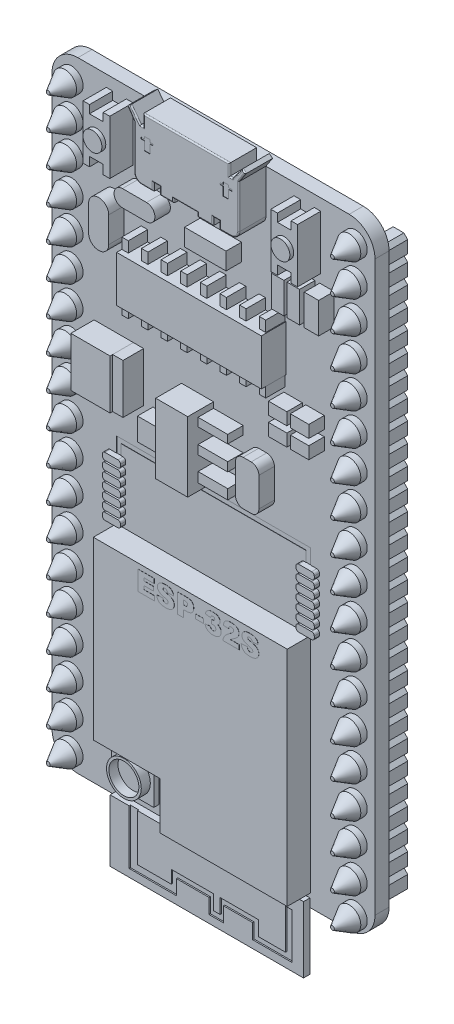
SolidWorks part; units mm, degrees
ref_plane "Front Plane" through (0, 0, 0) normal (0, 0, 1) x (1, 0, 0)
ref_plane "Top Plane" through (0, 0, 0) normal (0, 1, 0) x (1, 0, 0)
ref_plane "Right Plane" through (0, 0, 0) normal (1, 0, 0) x (0, 0, -1)
sketch "Sketch1" plane through (0, 0, 0) normal (0, 0, 1) x (1, 0, 0)
  line L1 (-10.5, 24) -> (10.5, 24)
  line L2 (-12.5, 22) -> (-12.5, -22)
  line L3 (-10.5, -24) -> (10.5, -24)
  line L4 (12.5, 22) -> (12.5, -22)
  line L5 (-12.5, 24) -> (12.5, -24) construction
  line L6 (-12.5, -24) -> (12.5, 24) construction
  arc A0 (-10.5, -24) -> (-12.5, -22) centre (-10.5, -22) cw
  arc A1 (10.5, -24) -> (12.5, -22) centre (10.5, -22) ccw
  arc A2 (12.5, 22) -> (10.5, 24) centre (10.5, 22) ccw
  arc A3 (-12.5, 22) -> (-10.5, 24) centre (-10.5, 22) cw
  point P0 (0, 0)
  dimension "D3" = 2
  dimension "D1" = 25
  dimension "D2" = 48
extrude "Boss-Extrude1" add sketch "Sketch1" along normal blind 1.09
sketch "Sketch2" plane through (0, 0, 1.09) normal (0, 0, 1) x (1, 0, 0)
  circle A0 centre (11.0006, 22.3012) radius 0.9
  dimension "D1" = 1.8
extrude "Boss-Extrude2" add sketch "Sketch2" along normal blind 1.8
chamfer "Chamfer1" distance 1.3 angle 30 1 edges at (11.9006, 22.3012, 2.89)
pattern_linear "LPattern1" count 19 spacing 2.5 along (0, -1, 0) count 2 spacing 22 along (-1, 0, 0) of "Boss-Extrude2", "Chamfer1"
sketch "Sketch3" plane through (0, 0, 1.09) normal (0, 0, 1) x (1, 0, 0)
  line L0 (0, 24) -> (0, -24)
  line L1 (-10.5, -24) -> (10.5, -24) construction
  line L2 (-12.5, 21.016) -> (12.5, 21.016)
  line L3 (12.5, -22) -> (12.5, 22) construction
  line L4 (-7.8022, 23.1053) -> (-7.8022, 22.482)
  line L5 (-8.3007, 23.1053) -> (-7.8022, 23.1053)
  line L6 (-8.3007, 23.1053) -> (-8.3007, 18.9267)
  line L7 (-8.3007, 18.9267) -> (-7.8022, 18.9267)
  line L8 (-6.2324, 23.1053) -> (-6.2324, 18.9267)
  line L9 (-8.3007, 23.1053) -> (-6.2324, 18.9267) construction
  line L10 (-8.3007, 18.9267) -> (-6.2324, 23.1053) construction
  line L11 (-7.8022, 22.482) -> (-6.7481, 22.482)
  line L12 (-6.7481, 22.482) -> (-6.7481, 23.1053)
  line L13 (-7.8022, 18.9267) -> (-7.8022, 19.6283)
  line L14 (-7.8022, 19.6283) -> (-6.7481, 19.6283)
  line L15 (-6.7481, 19.6283) -> (-6.7481, 18.9267)
  line L16 (-6.7481, 23.1053) -> (-6.2324, 23.1053)
  line L17 (-6.7481, 18.9267) -> (-6.2324, 18.9267)
  line L18 (8.3007, 18.9267) -> (6.2324, 23.1053) construction
  line L19 (8.3007, 23.1053) -> (6.2324, 18.9267) construction
  line L20 (6.7481, 18.9267) -> (6.2324, 18.9267)
  line L21 (6.7481, 23.1053) -> (6.2324, 23.1053)
  line L22 (6.7481, 19.6283) -> (6.7481, 18.9267)
  line L23 (7.8022, 19.6283) -> (6.7481, 19.6283)
  line L24 (7.8022, 18.9267) -> (7.8022, 19.6283)
  line L25 (6.7481, 22.482) -> (6.7481, 23.1053)
  line L26 (7.8022, 22.482) -> (6.7481, 22.482)
  line L27 (6.2324, 23.1053) -> (6.2324, 18.9267)
  line L28 (8.3007, 18.9267) -> (7.8022, 18.9267)
  line L29 (8.3007, 23.1053) -> (8.3007, 18.9267)
  line L30 (8.3007, 23.1053) -> (7.8022, 23.1053)
  line L31 (7.8022, 23.1053) -> (7.8022, 22.482)
  point P0 (-7.2666, 21.016)
  point P6 (0, 0)
  point P12 (0, 21.016)
  point P36 (7.2666, 21.016)
extrude "Boss-Extrude3" add sketch "Sketch3" along normal blind 1.8 contours L16 L12 L11 L4 L5 L6 L2 L8 | L15 L17 L8 L2 L6 L7 L13 L14 | L30 L31 L26 L25 L21 L27 L2 L29 | L29 L2 L27 L20 L22 L23 L24 L28
sketch "Sketch4" plane through (0, 0, 2.89) normal (0, 0, 1) x (1, 0, 0)
  line L0 (-7.2752, 22.482) -> (-7.2752, 19.6283) construction
  line L1 (-7.8022, 22.482) -> (-6.7481, 22.482) construction
  line L2 (-7.8022, 19.6283) -> (-6.7481, 19.6283) construction
  line L3 (-6.2324, 21.016) -> (-8.3007, 21.016) construction
  line L4 (-6.2324, 23.1053) -> (-6.2324, 18.9267) construction
  line L5 (-8.3007, 23.1053) -> (-8.3007, 18.9267) construction
  line L6 (0, 24) -> (0, 14.5911) construction
  line L7 (10.5, 24) -> (-10.5, 24) construction
  circle A0 centre (-7.2752, 21.0552) radius 0.7337
  circle A1 centre (7.2752, 21.0552) radius 0.7337
extrude "Boss-Extrude4" add sketch "Sketch4" along normal blind 0.3
sketch "Sketch5" plane through (0, 0, 1.09) normal (0, 0, 1) x (1, 0, 0)
  line L0 (-7.5049, -19.3526) -> (-2.3624, -19.3526)
  line L1 (-7.5049, -5.756) -> (7.5049, -5.756)
  line L2 (-7.5049, -5.756) -> (-7.5049, -19.3526)
  line L3 (-2.3624, -23.0043) -> (7.5049, -23.0043)
  line L4 (7.5049, -5.756) -> (7.5049, -23.0043)
  line L7 (-2.3624, -19.3526) -> (-2.3624, -23.0043)
  point P0 (0, -14.3801)
extrude "Boss-Extrude5" add sketch "Sketch5" along normal blind 1.8
sketch "Sketch6" plane through (0, 0, 2.89) normal (0, 0, 1) x (1, 0, 0)
  text T0 "ESP-32S" font "Arial Black" height 1.5
extrude "Boss-Extrude6" add sketch "Sketch6" along normal blind 0.01
sketch "Sketch7" plane through (0, 0, 1.09) normal (0, 0, 1) x (1, 0, 0)
  line L0 (-7.5049, -24) -> (-7.5049, -28.4731)
  line L1 (-10.5, -24) -> (10.5, -24) construction
  line L2 (-7.5049, -28.4731) -> (7.4655, -28.4731)
  line L3 (7.4655, -28.4731) -> (7.4655, -24)
  line L4 (-10.5, -24) -> (10.5, -24) construction
  line L5 (7.4655, -24) -> (7.4655, -23.3553)
  line L6 (7.4655, -23.3553) -> (-3.5697, -23.3553)
  line L7 (-3.5697, -23.3553) -> (-3.5697, -23.6776)
  line L8 (-3.5697, -23.6776) -> (-7.5049, -23.6776)
  line L9 (-7.5049, -23.6776) -> (-7.5049, -24)
extrude "Boss-Extrude7" add sketch "Sketch7" along normal blind 0.5
sketch "Sketch8" plane through (0, 0, 1.59) normal (0, 0, 1) x (1, 0, 0)
  line L0 (-6.0307, -23.6776) -> (-6.0307, -27.8761)
  line L1 (-3.5697, -23.6776) -> (-7.5049, -23.6776) construction
  line L2 (-6.0307, -27.8761) -> (-2.3778, -27.8761)
  line L3 (-2.3778, -27.8761) -> (-2.3778, -26.7276)
  line L4 (-2.3778, -26.7276) -> (0.1471, -26.7276)
  line L5 (0.1471, -26.7276) -> (0.1471, -27.8761)
  line L6 (0.1471, -27.8761) -> (1.2663, -27.8761)
  line L7 (1.2663, -27.8761) -> (1.2663, -26.7276)
  line L8 (1.2663, -26.7276) -> (3.5239, -26.7276)
  line L9 (3.5239, -26.7276) -> (3.5239, -27.8761)
  line L10 (3.5239, -27.8761) -> (6.5811, -27.8761)
  line L11 (6.5811, -27.8761) -> (6.5811, -24.3492)
  line L12 (6.5811, -24.3492) -> (6.0748, -24.3492)
  line L13 (6.0748, -24.3492) -> (6.0748, -27.4437)
  line L14 (6.0748, -27.4437) -> (3.9676, -27.4437)
  line L15 (3.9676, -27.4437) -> (3.9676, -26.3058)
  line L16 (3.9676, -26.3058) -> (1.0144, -26.3058)
  line L17 (1.0144, -26.3058) -> (1.0144, -27.4437)
  line L18 (1.0144, -27.4437) -> (0.5057, -27.4437)
  line L19 (0.5057, -27.4437) -> (0.5057, -26.3058)
  line L20 (0.5057, -26.3058) -> (-2.769, -26.3058)
  line L21 (-2.769, -26.3058) -> (-2.769, -27.3018)
  line L22 (-2.769, -27.3018) -> (-5.3686, -27.3018)
  line L23 (-5.3686, -27.3018) -> (-5.3686, -23.6776)
  line L24 (-5.3686, -23.6776) -> (-6.0307, -23.6776)
extrude "Cut-Extrude1" cut sketch "Sketch8" against normal blind 0.1
sketch "Sketch9" plane through (0, 0, 1.09) normal (0, 0, 1) x (1, 0, 0)
  line L1 (-7.4933, -19.7659) -> (-4.2275, -19.7659)
  line L2 (-7.4933, -19.7659) -> (-7.4933, -22.9384)
  line L3 (-7.4933, -22.9384) -> (-4.2275, -22.9384)
  line L4 (-4.2275, -19.7659) -> (-4.2275, -22.9384)
  line L5 (-7.4933, -19.7659) -> (-4.2275, -22.9384) construction
  line L6 (-7.4933, -22.9384) -> (-4.2275, -19.7659) construction
  point P0 (-5.8604, -21.3521)
extrude "Boss-Extrude8" add sketch "Sketch9" along normal blind 0.4
sketch "Sketch10" plane through (0, 0, 1.49) normal (0, 0, 1) x (1, 0, 0)
  circle A0 centre (-5.839, -21.4445) radius 1.3452
  circle A1 centre (-5.839, -21.4445) radius 1.1582
extrude "Boss-Extrude9" add sketch "Sketch10" along normal blind 0.7
sketch "Sketch11" plane through (0, 0, 1.09) normal (0, 0, 1) x (1, 0, 0)
  line L0 (0, 24) -> (0, 8.2029) construction
  line L1 (10.5, 24) -> (-10.5, 24) construction
  line L2 (-3.5676, 24) -> (-3.3361, 24)
  line L3 (-3.4554, 20.035) -> (-2.5545, 20.035)
  line L4 (-4.0554, 20.635) -> (-4.0554, 24)
  line L5 (-4.0554, 24) -> (-4.5727, 24.7847)
  line L6 (-4.5727, 24.7847) -> (-4.3141, 24.9814)
  line L7 (-4.3141, 24.9814) -> (-3.5676, 24)
  line L8 (-3.5676, 24) -> (-3.3361, 24)
  line L9 (-3.3361, 24) -> (-3.3361, 24.883)
  line L10 (-3.3361, 24.883) -> (3.3361, 24.883)
  line L11 (3.3361, 24) -> (3.3361, 24.883)
  line L12 (4.3141, 24.9814) -> (3.5676, 24)
  line L13 (4.5727, 24.7847) -> (4.3141, 24.9814)
  line L14 (4.0554, 24) -> (4.5727, 24.7847)
  line L15 (-3.5676, 24) -> (-3.3361, 24)
  line L16 (3.5676, 24) -> (3.3361, 24)
  line L17 (4.0554, 24) -> (4.0554, 20.635)
  line L18 (-2.5545, 20.035) -> (-2.5545, 20.635)
  line L19 (-2.5545, 20.635) -> (-2.0477, 20.635)
  line L20 (-2.0477, 20.635) -> (-2.0477, 20.035)
  line L21 (-0.9908, 20.035) -> (-0.9908, 20.3436)
  line L22 (-0.9908, 20.3436) -> (0.8553, 20.3436)
  line L23 (0.8553, 20.3436) -> (0.8553, 20.035)
  line L24 (2.0477, 20.635) -> (2.0477, 20.035)
  line L25 (2.5545, 20.635) -> (2.0477, 20.635)
  line L26 (2.5545, 20.035) -> (2.5545, 20.635)
  line L27 (-2.0477, 20.035) -> (-0.9908, 20.035)
  line L28 (2.5545, 20.035) -> (3.4554, 20.035)
  line L29 (0.8553, 20.035) -> (2.0477, 20.035)
  line L30 (3.5676, 24) -> (4.0554, 24) construction
  line L31 (-4.0554, 24) -> (-3.5676, 24) construction
  line L32 (-3.3361, 24) -> (0, 24) construction
  line L33 (3.3361, 24) -> (3.5676, 24)
  line L34 (0, 24) -> (3.3361, 24) construction
  arc A0 (3.4554, 20.035) -> (4.0554, 20.635) centre (3.4554, 20.635) ccw
  arc A1 (-4.0554, 20.635) -> (-3.4554, 20.035) centre (-3.4554, 20.635) ccw
  point P8 (0, 24)
  point P11 (0, 20.035)
  point P18 (0, 24.883)
  dimension "D1" = 0.6
extrude "Boss-Extrude10" add sketch "Sketch11" along normal blind 2.1 contours L4 A1 L3 L18 L19 L20 L27 L21 L22 L23 L29 L24 L25 L26 L28 A0 L17 L14 L13 L12 L16 L11 L10 L9 L2 L7 L6 L5
fillet "Fillet2" radius 0.1 28 edges at (-4.3141, 24.3923, 3.19) (-4.4434, 24.883, 3.19) (-3.9409, 24.4907, 3.19) (-3.4519, 24, 3.19) (-3.3361, 24.4415, 3.19) (0, 24.883, 3.19) (3.3361, 24.4415, 3.19) (3.4519, 24, 3.19) (3.9409, 24.4907, 3.19) (4.4434, 24.883, 3.19) (4.3141, 24.3923, 3.19) (4.0554, 22.3175, 3.19) (3.8797, 20.2107, 3.19) (3.0049, 20.035, 3.19) (2.5545, 20.335, 3.19) (2.3011, 20.635, 3.19) (2.0477, 20.335, 3.19) (1.4515, 20.035, 3.19) (0.8553, 20.1893, 3.19) (-0.0678, 20.3436, 3.19) (-0.9908, 20.1893, 3.19) (-1.5192, 20.035, 3.19) (-2.0477, 20.335, 3.19) (-2.3011, 20.635, 3.19) (-2.5545, 20.335, 3.19) (-3.0049, 20.035, 3.19) (-3.8797, 20.2107, 3.19) (-4.0554, 22.3175, 3.19)
sketch "Sketch12" plane through (0, 0, 3.19) normal (0, 0, 1) x (1, 0, 0)
  line L0 (0, 24.783) -> (0, 20.5643) construction
  line L1 (3.2361, 24.783) -> (-3.2361, 24.783) construction
  line L2 (-3.2452, 23.3939) -> (-2.8345, 23.3939)
  line L3 (-2.8345, 23.3939) -> (-2.8345, 23.2164)
  line L4 (-2.8345, 23.2164) -> (-2.5904, 23.2164)
  line L5 (-2.5904, 23.2164) -> (-2.5904, 23.0956)
  line L6 (-2.5904, 23.0956) -> (-2.8345, 23.0956)
  line L7 (-2.8345, 23.0956) -> (-2.8345, 22.4311)
  line L8 (-2.8345, 22.4311) -> (-3.2452, 22.4311)
  line L9 (-3.2452, 22.4311) -> (-3.2452, 23.0956)
  line L10 (-3.2452, 23.0956) -> (-3.5116, 23.0956)
  line L11 (-3.5116, 23.0956) -> (-3.5116, 23.2164)
  line L12 (-3.5116, 23.2164) -> (-3.2452, 23.2164)
  line L13 (-3.2452, 23.2164) -> (-3.2452, 23.3939)
  line L14 (2.5904, 23.2164) -> (2.5904, 23.0956)
  line L15 (2.8345, 23.2164) -> (2.5904, 23.2164)
  line L16 (2.8345, 23.3939) -> (2.8345, 23.2164)
  line L17 (3.2452, 23.3939) -> (2.8345, 23.3939)
  line L18 (3.2452, 23.2164) -> (3.2452, 23.3939)
  line L19 (3.5116, 23.2164) -> (3.2452, 23.2164)
  line L20 (3.5116, 23.0956) -> (3.5116, 23.2164)
  line L21 (3.2452, 23.0956) -> (3.5116, 23.0956)
  line L22 (3.2452, 22.4311) -> (3.2452, 23.0956)
  line L23 (2.8345, 22.4311) -> (3.2452, 22.4311)
  line L24 (2.8345, 23.0956) -> (2.8345, 22.4311)
  line L25 (2.5904, 23.0956) -> (2.8345, 23.0956)
extrude "Cut-Extrude2" cut sketch "Sketch12" against normal blind 0.02
sketch "Sketch13" plane through (0, 0, 1.09) normal (0, 0, 1) x (1, 0, 0)
  line L0 (0, 0) -> (0, 18.4602) construction
  line L2 (-5.5998, 14.3443) -> (5.5998, 14.3443)
  line L3 (-5.5998, 14.3443) -> (-5.5998, 10.7845)
  line L4 (-5.5998, 10.7845) -> (5.5998, 10.7845)
  line L5 (5.5998, 14.3443) -> (5.5998, 10.7845)
  line L6 (-5.5998, 14.3443) -> (5.5998, 10.7845) construction
  line L7 (-5.5998, 10.7845) -> (5.5998, 14.3443) construction
  point P3 (0, 12.5644)
extrude "Boss-Extrude11" add sketch "Sketch13" along normal blind 1.9
sketch "Sketch14" plane through (0, 0, 1.09) normal (0, 0, 1) x (1, 0, 0)
  line L0 (-5.5998, 14.3443) -> (-5.5998, 15.1718)
  line L1 (-5.5998, 15.1718) -> (-5.1003, 15.1718)
  line L2 (-5.1003, 15.1718) -> (-5.1003, 14.3443)
  line L3 (5.5998, 14.3443) -> (-5.5998, 14.3443) construction
  line L4 (-5.1003, 14.3443) -> (-5.5998, 14.3443)
  line L8 (5.5998, 10.7845) -> (5.5998, 14.3443)
  line L9 (5.5998, 14.3443) -> (-5.5998, 14.3443)
  line L10 (-5.5998, 14.3443) -> (-5.5998, 10.7845)
  line L11 (-5.5998, 10.7845) -> (5.5998, 10.7845)
  line L12 (5.5998, 10.7845) -> (5.5998, 14.3443)
  line L13 (5.5998, 14.3443) -> (-5.1003, 14.3443)
  line L14 (-5.5998, 14.3443) -> (-5.5998, 10.7845)
  line L15 (-5.5998, 10.7845) -> (5.5998, 10.7845)
  dimension "D1" = 0
extrude "Boss-Extrude12" add sketch "Sketch14" along normal blind 1.5 contours L4 L2 L1 L0
pattern_linear "LPattern2" count 8 spacing 1.52 along (1, 0, 0) count 2 spacing 4.4 along (0, -1, 0) of "Boss-Extrude12"
sketch "Sketch16" plane through (0, 0, 1.09) normal (0, 0, 1) x (1, 0, 0)
  line L0 (-2.4776, 5.1898) -> (-2.4776, 0.7784)
  line L1 (-2.4776, 0.7784) -> (0, 0.7784)
  line L2 (0, 0.7784) -> (0, 6.1793)
  line L3 (0, 6.1793) -> (-2.4776, 6.1793)
  line L4 (-2.4776, 6.1793) -> (-2.4776, 5.1898)
extrude "Boss-Extrude13" add sketch "Sketch16" along normal blind 2
sketch "Sketch17" plane through (0, 0, 1.09) normal (0, 0, 1) x (1, 0, 0)
  line L0 (-2.4776, 3.4788) -> (-4.689, 3.4788)
  line L1 (-2.4776, 6.1793) -> (-2.4776, 0.7784) construction
  line L2 (-4.689, 3.4788) -> (-4.689, 1.7455)
  line L3 (-4.689, 1.7455) -> (-2.4776, 1.7455)
  line L4 (-2.4776, 1.7455) -> (-2.4776, 3.4788)
  line L5 (0, 5.7377) -> (2.2974, 5.7377)
  line L6 (0, 0.7784) -> (0, 6.1793) construction
  line L7 (2.2974, 5.7377) -> (2.2974, 5.0961)
  line L8 (2.2974, 5.0961) -> (0, 5.0961)
  line L9 (0, 3.9079) -> (2.2974, 3.9079)
  line L10 (2.2974, 3.9079) -> (2.2974, 3.2188)
  line L11 (2.2974, 3.2188) -> (0, 3.2188)
  line L12 (0, 3.2188) -> (0, 3.9079)
  line L13 (0, 5.0961) -> (0, 5.7377)
  line L14 (0, 2.1019) -> (2.2974, 2.1019)
  line L15 (2.2974, 2.1019) -> (2.2974, 1.3415)
  line L16 (2.2974, 1.3415) -> (0, 1.3415)
  line L17 (0, 1.3415) -> (0, 2.1019)
extrude "Boss-Extrude14" add sketch "Sketch17" along normal blind 1.2
sketch "Sketch18" plane through (0, 0, 1.09) normal (0, 0, 1) x (1, 0, 0)
  line L0 (-5.8525, 17.5011) -> (-3.9854, 17.5011) construction
  line L1 (-5.8525, 18.1485) -> (-3.9854, 18.1485)
  line L2 (-5.8525, 16.8537) -> (-3.9854, 16.8537)
  line L3 (-7.6923, 15.8537) -> (-7.6923, 13.8535) construction
  line L4 (-6.9156, 15.8537) -> (-6.9156, 13.8535)
  line L5 (-8.469, 15.8537) -> (-8.469, 13.8535)
  line L7 (5.6746, 18.2413) -> (6.6484, 18.2413)
  line L8 (5.6746, 18.2413) -> (5.6746, 15.8537)
  line L9 (5.6746, 15.8537) -> (6.6484, 15.8537)
  line L10 (6.6484, 18.2413) -> (6.6484, 15.8537)
  line L11 (5.6746, 18.2413) -> (6.6484, 15.8537) construction
  line L12 (5.6746, 15.8537) -> (6.6484, 18.2413) construction
  line L13 (6.8765, 18.2413) -> (7.8606, 18.2413)
  line L14 (6.8765, 18.2413) -> (6.8765, 15.8537)
  line L15 (6.8765, 15.8537) -> (7.8606, 15.8537)
  line L16 (7.8606, 18.2413) -> (7.8606, 15.8537)
  line L17 (6.8765, 18.2413) -> (7.8606, 15.8537) construction
  line L18 (6.8765, 15.8537) -> (7.8606, 18.2413) construction
  line L19 (8.2224, 18.2413) -> (9.3369, 18.2413)
  line L20 (8.2224, 18.2413) -> (8.2224, 15.8537)
  line L21 (8.2224, 15.8537) -> (9.3369, 15.8537)
  line L22 (9.3369, 18.2413) -> (9.3369, 15.8537)
  line L23 (8.2224, 18.2413) -> (9.3369, 15.8537) construction
  line L24 (8.2224, 15.8537) -> (9.3369, 18.2413) construction
  line L25 (-1.0432, 17.9618) -> (2.1665, 17.9618)
  line L26 (-1.0432, 17.9618) -> (-1.0432, 16.6304)
  line L27 (-1.0432, 16.6304) -> (2.1665, 16.6304)
  line L28 (2.1665, 17.9618) -> (2.1665, 16.6304)
  line L29 (-1.0432, 17.9618) -> (2.1665, 16.6304) construction
  line L30 (-1.0432, 16.6304) -> (2.1665, 17.9618) construction
  line L31 (5.4465, 9.5479) -> (6.8765, 9.5479)
  line L32 (5.4465, 9.5479) -> (5.4465, 8.6021)
  line L33 (5.4465, 8.6021) -> (6.8765, 8.6021)
  line L34 (6.8765, 9.5479) -> (6.8765, 8.6021)
  line L35 (5.4465, 9.5479) -> (6.8765, 8.6021) construction
  line L36 (5.4465, 8.6021) -> (6.8765, 9.5479) construction
  line L37 (7.1463, 9.5479) -> (8.575, 9.5479)
  line L38 (7.1463, 9.5479) -> (7.1463, 8.6021)
  line L39 (7.1463, 8.6021) -> (8.575, 8.6021)
  line L40 (8.575, 9.5479) -> (8.575, 8.6021)
  line L41 (7.1463, 9.5479) -> (8.575, 8.6021) construction
  line L42 (7.1463, 8.6021) -> (8.575, 9.5479) construction
  line L43 (5.4465, 8.1204) -> (6.8765, 8.1204)
  line L44 (5.4465, 8.1204) -> (5.4465, 7.1736)
  line L45 (5.4465, 7.1736) -> (6.8765, 7.1736)
  line L46 (6.8765, 8.1204) -> (6.8765, 7.1736)
  line L47 (5.4465, 8.1204) -> (6.8765, 7.1736) construction
  line L48 (5.4465, 7.1736) -> (6.8765, 8.1204) construction
  line L49 (7.1463, 8.1204) -> (8.575, 8.1204)
  line L50 (7.1463, 8.1204) -> (7.1463, 7.1736)
  line L51 (7.1463, 7.1736) -> (8.575, 7.1736)
  line L52 (8.575, 8.1204) -> (8.575, 7.1736)
  line L53 (7.1463, 8.1204) -> (8.575, 7.1736) construction
  line L54 (7.1463, 7.1736) -> (8.575, 8.1204) construction
  line L55 (3.4926, 4.8046) -> (4.1148, 4.8046)
  line L56 (2.8926, 4.2046) -> (2.8926, 1.9487)
  line L57 (3.4926, 1.3487) -> (4.1148, 1.3487)
  line L58 (4.7148, 4.2046) -> (4.7148, 1.9487)
  line L59 (2.8926, 4.8046) -> (4.7148, 1.3487) construction
  line L60 (2.8926, 1.3487) -> (4.7148, 4.8046) construction
  arc A0 (-5.8525, 18.1485) -> (-5.8525, 16.8537) centre (-5.8525, 17.5011) ccw
  arc A1 (-3.9854, 16.8537) -> (-3.9854, 18.1485) centre (-3.9854, 17.5011) ccw
  arc A2 (-6.9156, 15.8537) -> (-8.469, 15.8537) centre (-7.6923, 15.8537) ccw
  arc A3 (-8.469, 13.8535) -> (-6.9156, 13.8535) centre (-7.6923, 13.8535) ccw
  arc A4 (3.4926, 1.3487) -> (2.8926, 1.9487) centre (3.4926, 1.9487) cw
  arc A5 (4.1148, 1.3487) -> (4.7148, 1.9487) centre (4.1148, 1.9487) ccw
  arc A6 (4.7148, 4.2046) -> (4.1148, 4.8046) centre (4.1148, 4.2046) ccw
  arc A7 (2.8926, 4.2046) -> (3.4926, 4.8046) centre (3.4926, 4.2046) cw
  point P2 (-4.9189, 17.5011)
  point P7 (-7.6923, 14.8536)
  point P14 (6.1615, 17.0475)
  point P19 (7.3686, 17.0475)
  point P24 (8.7797, 17.0475)
  point P29 (0.5617, 17.2961)
  point P34 (6.1615, 9.075)
  point P39 (7.8606, 9.075)
  point P44 (6.1615, 7.647)
  point P49 (7.8606, 7.647)
  point P54 (3.8037, 3.0767)
  dimension "D1" = 0.6
extrude "Boss-Extrude15" add sketch "Sketch18" along normal blind 1.2
sketch "Sketch19" plane through (0, 0, 1.09) normal (0, 0, 1) x (1, 0, 0)
  line L1 (-7.5049, -0.6837) -> (7.5396, -0.6837)
  line L3 (7.5049, -5.756) -> (-7.5049, -5.756)
  line L4 (0, -5.756) -> (0.0174, -0.6837) construction
  line L5 (-8.0085, -1.6867) -> (-7.0014, -1.6867)
  line L6 (-8.0085, -1.0167) -> (-7.0014, -1.0167)
  line L7 (-8.2085, -1.2167) -> (-8.2085, -1.3543)
  line L8 (-8.0085, -1.5543) -> (-7.0014, -1.5543)
  line L9 (-6.8014, -1.2167) -> (-6.8014, -1.3543)
  line L10 (-6.8014, -1.8867) -> (-6.8014, -2.0243)
  line L11 (-8.0085, -2.2243) -> (-7.0014, -2.2243)
  line L12 (-8.2085, -1.8867) -> (-8.2085, -2.0243)
  line L13 (-8.0085, -2.3567) -> (-7.0014, -2.3567)
  line L14 (-6.8014, -2.5567) -> (-6.8014, -2.6943)
  line L15 (-8.0085, -2.8943) -> (-7.0014, -2.8943)
  line L16 (-8.2085, -2.5567) -> (-8.2085, -2.6943)
  line L17 (-8.0085, -3.0267) -> (-7.0014, -3.0267)
  line L18 (-6.8014, -3.2267) -> (-6.8014, -3.3643)
  line L19 (-8.0085, -3.5643) -> (-7.0014, -3.5643)
  line L20 (-8.2085, -3.2267) -> (-8.2085, -3.3643)
  line L21 (-8.0085, -3.6967) -> (-7.0014, -3.6967)
  line L22 (-6.8014, -3.8967) -> (-6.8014, -4.0343)
  line L23 (-8.0085, -4.2343) -> (-7.0014, -4.2343)
  line L24 (-8.2085, -3.8967) -> (-8.2085, -4.0343)
  line L25 (-8.0085, -4.3667) -> (-7.0014, -4.3667)
  line L26 (-6.8014, -4.5667) -> (-6.8014, -4.7043)
  line L27 (-8.0085, -4.9043) -> (-7.0014, -4.9043)
  line L28 (-8.2085, -4.5667) -> (-8.2085, -4.7043)
  line L29 (-8.0085, -5.0367) -> (-7.0014, -5.0367)
  line L30 (-6.8014, -5.2367) -> (-6.8014, -5.3743)
  line L31 (-8.0085, -5.5743) -> (-7.0014, -5.5743)
  line L32 (-8.2085, -5.2367) -> (-8.2085, -5.3743)
  line L33 (6.9915, -1.6867) -> (7.9986, -1.6867)
  line L34 (8.1986, -1.8867) -> (8.1986, -2.0243)
  line L35 (6.9915, -2.2243) -> (7.9986, -2.2243)
  line L36 (6.7915, -1.8867) -> (6.7915, -2.0243)
  line L37 (6.9915, -2.3567) -> (7.9986, -2.3567)
  line L38 (8.1986, -2.5567) -> (8.1986, -2.6943)
  line L39 (6.9915, -2.8943) -> (7.9986, -2.8943)
  line L40 (6.7915, -2.5567) -> (6.7915, -2.6943)
  line L41 (6.9915, -3.0267) -> (7.9986, -3.0267)
  line L42 (8.1986, -3.2267) -> (8.1986, -3.3643)
  line L43 (6.9915, -3.5643) -> (7.9986, -3.5643)
  line L44 (6.7915, -3.2267) -> (6.7915, -3.3643)
  line L45 (6.9915, -3.6967) -> (7.9986, -3.6967)
  line L46 (8.1986, -3.8967) -> (8.1986, -4.0343)
  line L47 (6.9915, -4.2343) -> (7.9986, -4.2343)
  line L48 (6.7915, -3.8967) -> (6.7915, -4.0343)
  line L49 (6.9915, -4.3667) -> (7.9986, -4.3667)
  line L50 (8.1986, -4.5667) -> (8.1986, -4.7043)
  line L51 (6.9915, -4.9043) -> (7.9986, -4.9043)
  line L52 (6.7915, -4.5667) -> (6.7915, -4.7043)
  line L53 (6.9915, -5.0367) -> (7.9986, -5.0367)
  line L54 (8.1986, -5.2367) -> (8.1986, -5.3743)
  line L55 (6.9915, -5.5743) -> (7.9986, -5.5743)
  line L56 (6.7915, -5.2367) -> (6.7915, -5.3743)
  line L57 (6.9915, -1.0167) -> (7.9986, -1.0167)
  line L58 (8.1986, -1.2167) -> (8.1986, -1.3543)
  line L59 (6.9915, -1.5543) -> (7.9986, -1.5543)
  line L60 (6.7915, -1.2167) -> (6.7915, -1.3543)
  line L61 (-8.0085, -1.0167) -> (-8.0085, -1.6867) construction
  line L62 (-8.0085, -1.0167) -> (6.9915, -1.0167) construction
  arc A0 (-8.0085, -1.5543) -> (-8.2085, -1.3543) centre (-8.0085, -1.3543) cw
  arc A1 (-7.0014, -1.5543) -> (-6.8014, -1.3543) centre (-7.0014, -1.3543) ccw
  arc A2 (-6.8014, -1.2167) -> (-7.0014, -1.0167) centre (-7.0014, -1.2167) ccw
  arc A3 (-8.2085, -1.2167) -> (-8.0085, -1.0167) centre (-8.0085, -1.2167) cw
  arc A4 (-6.8014, -1.8867) -> (-7.0014, -1.6867) centre (-7.0014, -1.8867) ccw
  arc A5 (-7.0014, -2.2243) -> (-6.8014, -2.0243) centre (-7.0014, -2.0243) ccw
  arc A6 (-8.0085, -2.2243) -> (-8.2085, -2.0243) centre (-8.0085, -2.0243) cw
  arc A7 (-8.2085, -1.8867) -> (-8.0085, -1.6867) centre (-8.0085, -1.8867) cw
  arc A8 (-6.8014, -2.5567) -> (-7.0014, -2.3567) centre (-7.0014, -2.5567) ccw
  arc A9 (-7.0014, -2.8943) -> (-6.8014, -2.6943) centre (-7.0014, -2.6943) ccw
  arc A10 (-8.0085, -2.8943) -> (-8.2085, -2.6943) centre (-8.0085, -2.6943) cw
  arc A11 (-8.2085, -2.5567) -> (-8.0085, -2.3567) centre (-8.0085, -2.5567) cw
  arc A12 (-6.8014, -3.2267) -> (-7.0014, -3.0267) centre (-7.0014, -3.2267) ccw
  arc A13 (-7.0014, -3.5643) -> (-6.8014, -3.3643) centre (-7.0014, -3.3643) ccw
  arc A14 (-8.0085, -3.5643) -> (-8.2085, -3.3643) centre (-8.0085, -3.3643) cw
  arc A15 (-8.2085, -3.2267) -> (-8.0085, -3.0267) centre (-8.0085, -3.2267) cw
  arc A16 (-6.8014, -3.8967) -> (-7.0014, -3.6967) centre (-7.0014, -3.8967) ccw
  arc A17 (-7.0014, -4.2343) -> (-6.8014, -4.0343) centre (-7.0014, -4.0343) ccw
  arc A18 (-8.0085, -4.2343) -> (-8.2085, -4.0343) centre (-8.0085, -4.0343) cw
  arc A19 (-8.2085, -3.8967) -> (-8.0085, -3.6967) centre (-8.0085, -3.8967) cw
  arc A20 (-6.8014, -4.5667) -> (-7.0014, -4.3667) centre (-7.0014, -4.5667) ccw
  arc A21 (-7.0014, -4.9043) -> (-6.8014, -4.7043) centre (-7.0014, -4.7043) ccw
  arc A22 (-8.0085, -4.9043) -> (-8.2085, -4.7043) centre (-8.0085, -4.7043) cw
  arc A23 (-8.2085, -4.5667) -> (-8.0085, -4.3667) centre (-8.0085, -4.5667) cw
  arc A24 (-6.8014, -5.2367) -> (-7.0014, -5.0367) centre (-7.0014, -5.2367) ccw
  arc A25 (-7.0014, -5.5743) -> (-6.8014, -5.3743) centre (-7.0014, -5.3743) ccw
  arc A26 (-8.0085, -5.5743) -> (-8.2085, -5.3743) centre (-8.0085, -5.3743) cw
  arc A27 (-8.2085, -5.2367) -> (-8.0085, -5.0367) centre (-8.0085, -5.2367) cw
  arc A28 (8.1986, -1.8867) -> (7.9986, -1.6867) centre (7.9986, -1.8867) ccw
  arc A29 (7.9986, -2.2243) -> (8.1986, -2.0243) centre (7.9986, -2.0243) ccw
  arc A30 (6.9915, -2.2243) -> (6.7915, -2.0243) centre (6.9915, -2.0243) cw
  arc A31 (6.7915, -1.8867) -> (6.9915, -1.6867) centre (6.9915, -1.8867) cw
  arc A32 (8.1986, -2.5567) -> (7.9986, -2.3567) centre (7.9986, -2.5567) ccw
  arc A33 (7.9986, -2.8943) -> (8.1986, -2.6943) centre (7.9986, -2.6943) ccw
  arc A34 (6.9915, -2.8943) -> (6.7915, -2.6943) centre (6.9915, -2.6943) cw
  arc A35 (6.7915, -2.5567) -> (6.9915, -2.3567) centre (6.9915, -2.5567) cw
  arc A36 (8.1986, -3.2267) -> (7.9986, -3.0267) centre (7.9986, -3.2267) ccw
  arc A37 (7.9986, -3.5643) -> (8.1986, -3.3643) centre (7.9986, -3.3643) ccw
  arc A38 (6.9915, -3.5643) -> (6.7915, -3.3643) centre (6.9915, -3.3643) cw
  arc A39 (6.7915, -3.2267) -> (6.9915, -3.0267) centre (6.9915, -3.2267) cw
  arc A40 (8.1986, -3.8967) -> (7.9986, -3.6967) centre (7.9986, -3.8967) ccw
  arc A41 (7.9986, -4.2343) -> (8.1986, -4.0343) centre (7.9986, -4.0343) ccw
  arc A42 (6.9915, -4.2343) -> (6.7915, -4.0343) centre (6.9915, -4.0343) cw
  arc A43 (6.7915, -3.8967) -> (6.9915, -3.6967) centre (6.9915, -3.8967) cw
  arc A44 (8.1986, -4.5667) -> (7.9986, -4.3667) centre (7.9986, -4.5667) ccw
  arc A45 (7.9986, -4.9043) -> (8.1986, -4.7043) centre (7.9986, -4.7043) ccw
  arc A46 (6.9915, -4.9043) -> (6.7915, -4.7043) centre (6.9915, -4.7043) cw
  arc A47 (6.7915, -4.5667) -> (6.9915, -4.3667) centre (6.9915, -4.5667) cw
  arc A48 (8.1986, -5.2367) -> (7.9986, -5.0367) centre (7.9986, -5.2367) ccw
  arc A49 (7.9986, -5.5743) -> (8.1986, -5.3743) centre (7.9986, -5.3743) ccw
  arc A50 (6.9915, -5.5743) -> (6.7915, -5.3743) centre (6.9915, -5.3743) cw
  arc A51 (6.7915, -5.2367) -> (6.9915, -5.0367) centre (6.9915, -5.2367) cw
  arc A52 (8.1986, -1.2167) -> (7.9986, -1.0167) centre (7.9986, -1.2167) ccw
  arc A53 (7.9986, -1.5543) -> (8.1986, -1.3543) centre (7.9986, -1.3543) ccw
  arc A54 (6.9915, -1.5543) -> (6.7915, -1.3543) centre (6.9915, -1.3543) cw
  arc A55 (6.7915, -1.2167) -> (6.9915, -1.0167) centre (6.9915, -1.2167) cw
  point P8 (-7.5049, -1.2855)
  dimension "D1" = 0.2
  dimension "D4" = 90
  dimension "D2" = 7
  dimension "D3" = 2
extrude "Boss-Extrude16" add sketch "Sketch19" along normal blind 0.4 contours A3 L7 A0 L8 A1 L9 A2 L6 | A7 L12 A6 L11 A5 L10 A4 L5 | A11 L16 A10 L15 A9 L14 A8 L13 | A15 L20 A14 L19 A13 L18 A12 L17 | A19 L24 A18 L23 A17 L22 A16 L21 | A23 L28 A22 L27 A21 L26 A20 L25 | A27 L32 A26 L31 A25 L30 A24 L29 | A55 L60 A54 L59 A53 L58 A52 L57 | A31 L36 A30 L35 A29 L34 A28 L33 | A35 L40 A34 L39 A33 L38 A32 L37 | A39 L44 A38 L43 A37 L42 A36 L41 | A47 L52 A46 L51 A45 L50 A44 L49 | A51 L56 A50 L55 A49 L54 A48 L53 | L45 A40 L46 A41 L47 A42 L48 A43
sketch "Sketch20" plane through (0, 0, 1.09) normal (0, 0, 1) x (1, 0, 0)
  line L0 (0, -5.756) -> (0, -0.3275) construction
  line L1 (7.5049, -5.756) -> (-7.5049, -5.756) construction
  line L2 (-7.5049, -1.0167) -> (-7.5049, 0.1383)
  line L3 (-8.0085, -1.0167) -> (-7.0014, -1.0167) construction
  line L4 (-7.5049, 0.1383) -> (7.5049, 0.1383)
  line L5 (0, 0.1383) -> (0, -0.2083) construction
  line L6 (7.1514, -0.2083) -> (-7.1514, -0.2083)
  line L7 (-7.1514, -0.2083) -> (-7.1514, -1.0167)
  line L8 (-7.1514, -1.0167) -> (-7.5049, -1.0167)
  line L9 (7.1514, -0.2083) -> (7.1514, -1.0167)
  line L10 (7.5049, -1.0167) -> (7.5049, 0.1383)
  line L11 (7.1514, -1.0167) -> (7.5049, -1.0167)
extrude "Cut-Extrude3" cut sketch "Sketch20" against normal blind 0.02
sketch "Sketch21" plane through (0, 0, 1.09) normal (0, 0, 1) x (1, 0, 0)
  line L1 (-9.2461, 7.0441) -> (-6.2086, 7.0441)
  line L2 (-9.2461, 7.0441) -> (-9.2461, 3.2177)
  line L3 (-9.2461, 3.2177) -> (-6.2086, 3.2177)
  line L4 (-6.2086, 7.0441) -> (-6.2086, 3.2177)
  line L5 (-9.2461, 7.0441) -> (-6.2086, 3.2177) construction
  line L6 (-9.2461, 3.2177) -> (-6.2086, 7.0441) construction
  point P0 (-7.7274, 5.1309)
extrude "Boss-Extrude17" add sketch "Sketch21" along normal blind 1.8
sketch "Sketch22" plane through (0, 0, 1.09) normal (0, 0, 1) x (1, 0, 0)
  line L0 (-6.2086, 7.0441) -> (-5.4079, 7.0441)
  line L1 (-5.4079, 7.0441) -> (-5.4079, 3.2177)
  line L2 (-5.4079, 3.2177) -> (-6.2086, 3.2177)
  line L3 (-6.2086, 3.2177) -> (-6.2086, 7.0441)
extrude "Boss-Extrude18" add sketch "Sketch22" along normal blind 1.6 separate body
sketch "Sketch23" plane through (0, 0, 0) normal (0, 0, -1) x (-1, 0, 0)
  line L0 (-11.8448, 21.9778) -> (-11.0133, 21.9778)
  line L1 (-10.7133, 21.6778) -> (-10.7133, 20.7753)
  line L2 (-10.7133, 20.7753) -> (-11.0855, 20.4031)
  line L3 (-11.0855, 20.4031) -> (-11.8299, 20.4031)
  line L4 (-11.8299, 20.4031) -> (-12.1448, 20.718)
  line L5 (-12.1448, 20.718) -> (-12.1448, 21.6778)
  line L6 (-12.1448, 21.9578) -> (-12.1248, 21.9778)
  line L7 (-10.7333, 21.9778) -> (-10.7133, 21.9578)
  line L8 (-12.1448, 21.6778) -> (-11.8448, 21.9778)
  line L9 (-11.0133, 21.9778) -> (-10.7133, 21.6778)
  point P0 (-12.1448, 21.9778)
  point P1 (-10.7133, 21.9778)
  point P12 (-12.1448, 21.9778)
  point P15 (-10.7133, 21.9778)
extrude "Boss-Extrude19" add sketch "Sketch23" along normal blind 1.8 contours L9 L0 L8 L5 L4 L3 L2 L1
pattern_linear "LPattern3" count 29 spacing 1.52 along (0, -1, 0) count 2 spacing 22.9 along (-1, 0, 0) of "Boss-Extrude19"
